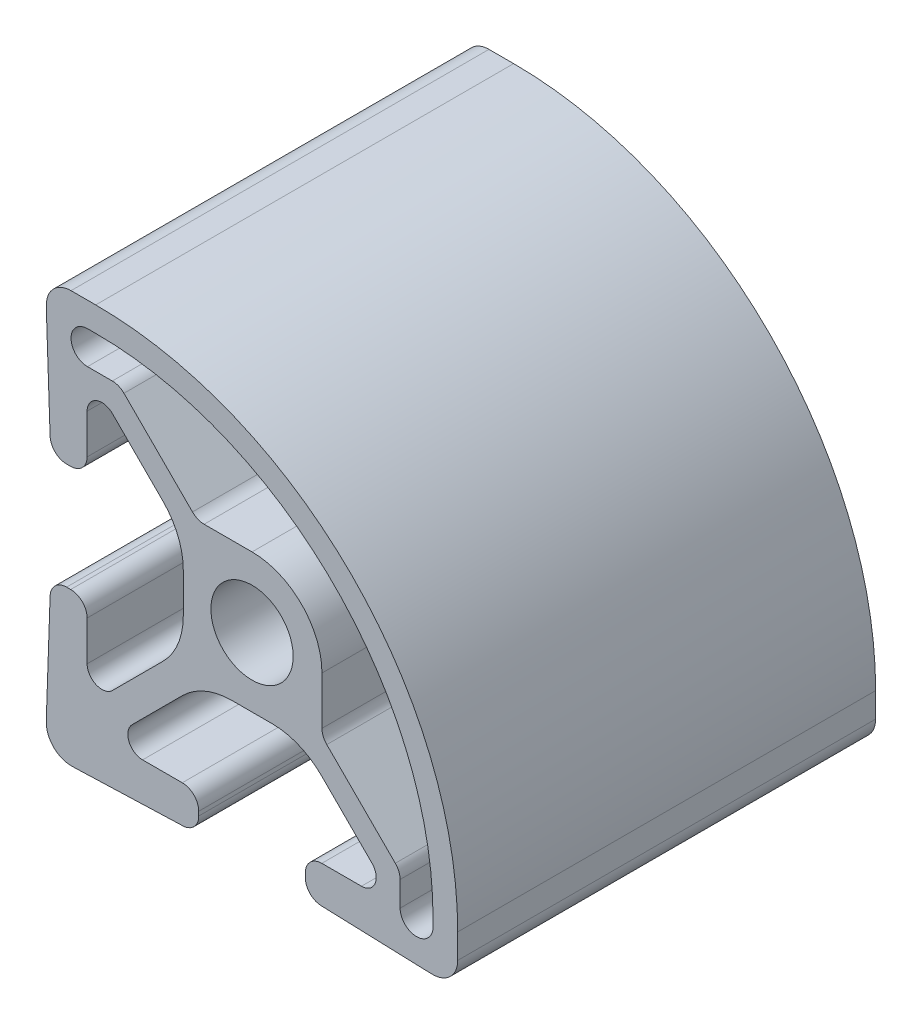
SolidWorks part; units mm, degrees
material "6061 Alloy"
ref_plane "Front" through (0, 0, 0) normal (0, 0, 1) x (1, 0, 0)
ref_plane "Top" through (0, 0, 0) normal (0, 1, 0) x (1, 0, 0)
ref_plane "Right" through (0, 0, 0) normal (1, 0, 0) x (0, 0, -1)
sketch "Sketch1" plane through (0, 0, 0) normal (0, 0, 1) x (1, 0, 0)
  line L0 (4.25, 0) -> (4.25, -2.9125)
  line L1 (-2.9125, 4.25) -> (0, 4.25)
  line L2 (4.5429, -3.6196) -> (8.7071, -7.7838)
  line L3 (-7.7838, 8.7071) -> (-3.6196, 4.5429)
  line L4 (9, -8.4909) -> (9, -10)
  line L5 (-10, 9) -> (-8.4909, 9)
  line L6 (11, -10) -> (11, -9.5)
  line L7 (-9.5, 11) -> (-10, 11)
  line L8 (1.2205, -4.179) -> (-1.2205, -4.179)
  line L9 (7.2865, -8.4846) -> (4.2257, -5.4238)
  line L10 (-4.2257, -5.4238) -> (-7.2865, -8.4846)
  line L11 (4.24, -10.021) -> (6.6501, -10.021)
  line L12 (-6.6501, -10.021) -> (-4.24, -10.021)
  line L13 (3.24, -11.2724) -> (3.24, -11.021)
  line L14 (-3.24, -11.021) -> (-3.24, -11.2724)
  line L15 (4.2051, -12.2718) -> (10.74, -12.5)
  line L16 (-10.74, -12.5) -> (-4.2051, -12.2718)
  line L17 (10.74, -12.5) -> (11, -12.5)
  line L18 (-11, -12.5) -> (-10.74, -12.5)
  line L19 (12.5, -11) -> (12.5, -9.5)
  line L20 (-12.5, -10.74) -> (-12.5, -11)
  line L21 (-12.2718, -4.2051) -> (-12.5, -10.74)
  line L22 (-9.5, 12.5) -> (-11, 12.5)
  line L23 (-11.2724, -3.24) -> (-11.021, -3.24)
  line L24 (-12.5, 11) -> (-12.5, 10.74)
  line L25 (-12.5, 10.74) -> (-12.2718, 4.2051)
  line L26 (-10.021, -4.24) -> (-10.021, -6.6501)
  line L27 (-11.021, 3.24) -> (-11.2724, 3.24)
  line L28 (-8.4846, -7.2865) -> (-5.4238, -4.2257)
  line L29 (-10.021, 6.6501) -> (-10.021, 4.24)
  line L30 (-4.179, -1.2205) -> (-4.179, 1.2205)
  line L31 (-5.4238, 4.2257) -> (-8.4846, 7.2865)
  arc A0 (4.25, 0) -> (0, 4.25) centre (0, 0) ccw
  arc A1 (4.25, -2.9125) -> (4.5429, -3.6196) centre (5.25, -2.9125) ccw
  arc A2 (-3.6196, 4.5429) -> (-2.9125, 4.25) centre (-2.9125, 5.25) ccw
  arc A3 (9, -8.4909) -> (8.7071, -7.7838) centre (8, -8.4909) ccw
  arc A4 (-7.7838, 8.7071) -> (-8.4909, 9) centre (-8.4909, 8) ccw
  arc A5 (9, -10) -> (11, -10) centre (10, -10) ccw
  arc A6 (-10, 11) -> (-10, 9) centre (-10, 10) ccw
  arc A7 (11, -9.5) -> (-9.5, 11) centre (-9.5, -9.5) ccw
  arc A8 (4.2257, -5.4238) -> (1.2205, -4.179) centre (1.2205, -8.429) ccw
  arc A9 (-1.2205, -4.179) -> (-4.2257, -5.4238) centre (-1.2205, -8.429) ccw
  arc A10 (6.6501, -10.021) -> (7.2865, -8.4846) centre (6.6501, -9.121) ccw
  arc A11 (-7.2865, -8.4846) -> (-6.6501, -10.021) centre (-6.6501, -9.121) ccw
  arc A12 (4.24, -10.021) -> (3.24, -11.021) centre (4.24, -11.021) ccw
  arc A13 (-3.24, -11.021) -> (-4.24, -10.021) centre (-4.24, -11.021) ccw
  arc A14 (3.24, -11.2724) -> (4.2051, -12.2718) centre (4.24, -11.2724) ccw
  arc A15 (-4.2051, -12.2718) -> (-3.24, -11.2724) centre (-4.24, -11.2724) ccw
  arc A16 (11, -12.5) -> (12.5, -11) centre (11, -11) ccw
  arc A17 (-12.5, -11) -> (-11, -12.5) centre (-11, -11) ccw
  arc A18 (12.5, -9.5) -> (-9.5, 12.5) centre (-9.5, -9.5) ccw
  arc A19 (-11.2724, -3.24) -> (-12.2718, -4.2051) centre (-11.2724, -4.24) ccw
  arc A20 (-11, 12.5) -> (-12.5, 11) centre (-11, 11) ccw
  arc A21 (-10.021, -4.24) -> (-11.021, -3.24) centre (-11.021, -4.24) ccw
  arc A22 (-12.2718, 4.2051) -> (-11.2724, 3.24) centre (-11.2724, 4.24) ccw
  arc A23 (-10.021, -6.6501) -> (-8.4846, -7.2865) centre (-9.121, -6.6501) ccw
  arc A24 (-11.021, 3.24) -> (-10.021, 4.24) centre (-11.021, 4.24) ccw
  arc A25 (-5.4238, -4.2257) -> (-4.179, -1.2205) centre (-8.429, -1.2205) ccw
  arc A26 (-8.4846, 7.2865) -> (-10.021, 6.6501) centre (-9.121, 6.6501) ccw
  arc A27 (-4.179, 1.2205) -> (-5.4238, 4.2257) centre (-8.429, 1.2205) ccw
  circle A28 centre (0, 0) radius 2.5
extrude "Extrude1" add sketch "Sketch1" along normal blind 25.4
